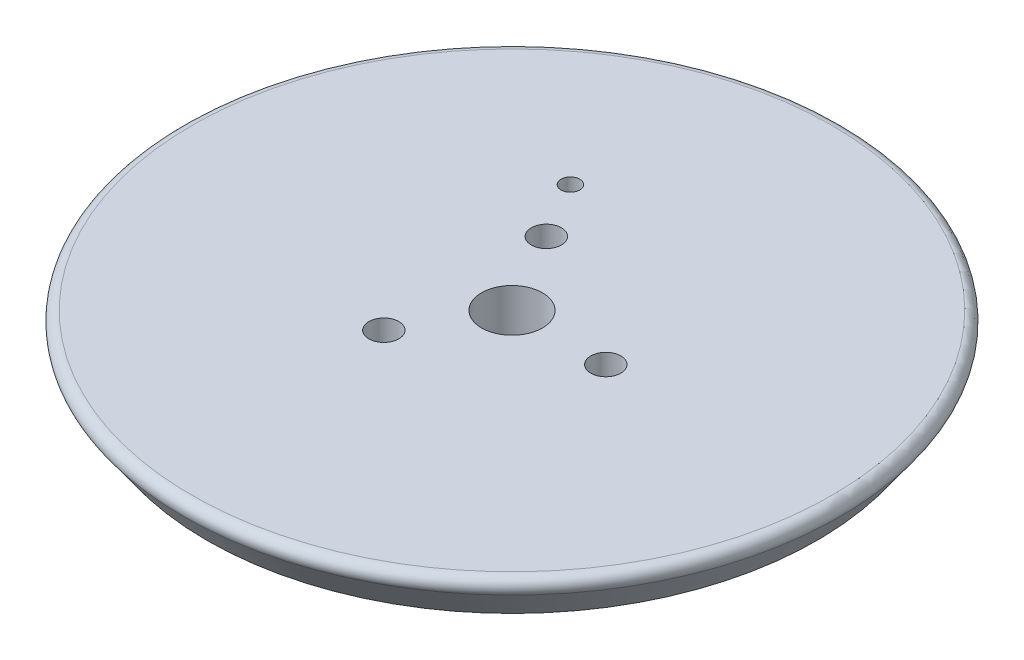
SolidWorks part; units mm, degrees
ref_plane "Plan de face" through (0, 0, 0) normal (0, 0, 1) x (1, 0, 0)
ref_plane "Plan de dessus" through (0, 0, 0) normal (0, 1, 0) x (1, 0, 0)
ref_plane "Plan de droite" through (0, 0, 0) normal (1, 0, 0) x (0, 0, -1)
sketch "Esquisse1" plane through (0, 0, 0) normal (0, 0, 1) x (1, 0, 0)
  line L0 (0, 33.1663) -> (0, -43.5308) construction
  line L1 (0, 0) -> (36.0717, 0)
  line L2 (36.0717, 0) -> (32.5, -5)
  line L3 (32.5, -5) -> (15, -5)
  line L4 (15, -5) -> (15, -6.4)
  line L5 (15, -6.4) -> (5.25, -6.4)
  line L6 (5.25, -6.4) -> (3.25, -8.4)
  line L7 (3.25, -8.4) -> (0, -8.4)
  line L8 (0, -8.4) -> (0, 0)
  point P5 (1.625, -8.4)
  dimension "D1" = 32.5
  dimension "D2" = 5
  dimension "D3" = 1.4
  dimension "D4" = 2
  dimension "D5" = 45
  dimension "D6" = 3.25
  dimension "D7" = 15
  dimension "D8" = 54.46
revolve "Révolution1" add sketch "Esquisse1" angle 360 about L0
fillet "Congé1" radius 1 1 edges at (0, 0, 36.0717)
sketch "Esquisse2" plane through (0, 0, 0) normal (0, 1, 0) x (1, 0, 0)
  line L0 (0, 0) -> (10, 0) construction
  line L1 (0, 0) -> (-5, 8.6603) construction
  line L2 (-5, 8.6603) -> (-11.1696, 19.3462) construction
  circle A0 centre (0, 0) radius 3.25
  circle A1 centre (10, 0) radius 1.6
  circle A2 centre (-5, -8.6603) radius 1.6
  circle A3 centre (-5, 8.6603) radius 1.6
  circle A4 centre (-8.5, 14.7224) radius 1
  point P11 (0, 0)
  dimension "D1" = 6.5
  dimension "D2" = 3.2
  dimension "D3" = 10
  dimension "D5" = 17
  dimension "D4" = 3
extrude "Enlèv. mat.-Extru.1" cut sketch "Esquisse2" against normal up to next
